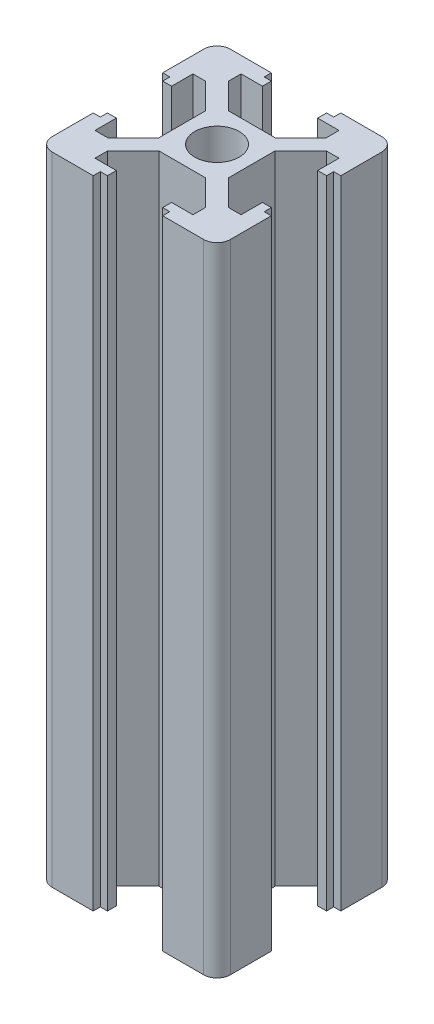
SolidWorks part; units mm, degrees
material "6063-O"
ref_plane "Front Plane" through (0, 0, 0) normal (0, 0, 1) x (1, 0, 0)
ref_plane "Top Plane" through (0, 0, 0) normal (0, 1, 0) x (1, 0, 0)
ref_plane "Right Plane" through (0, 0, 0) normal (1, 0, 0) x (0, 0, -1)
sketch "Sketch1" plane through (0, 0, 0) normal (0, 1, 0) x (1, 0, 0)
  line L0 (0, 14.5399) -> (0, 10) construction
  line L1 (-16.8658, 0) -> (2.5, 0) construction
  line L2 (13.2784, 3.9) -> (3.9, 3.9) construction
  line L3 (0, 0) -> (2.5, 0)
  line L4 (0, 0) -> (0, 2.5)
  line L5 (3.9, 10) -> (8.5, 10)
  line L6 (9.2, 0) -> (16.4291, 0) construction
  line L7 (-2.63, 3.9) -> (2.63, 3.9)
  line L9 (2.5491, 3.9) -> (2.63, 3.9)
  line L10 (3.9, 0) -> (3.9, 2.63)
  line L11 (13.2784, 3.1) -> (2.5491, 3.1) construction
  line L12 (8.2, 7.5573) -> (8.2, -3.0868) construction
  line L13 (9.2, 7.2593) -> (9.2, -8.1534) construction
  line L14 (10, 3.9) -> (9.2, 3.9)
  line L15 (9.2, 3.9) -> (9.2, 3.1)
  line L16 (9.2, 3.1) -> (8.2, 3.1)
  line L17 (8.2, 3.1) -> (8.2, 5.5)
  line L18 (8.2, 5.5) -> (6.77, 5.5)
  line L19 (6.77, 5.5) -> (3.9, 2.63)
  line L20 (5.0973, 5.5) -> (13.0082, 5.5) construction
  line L21 (3.1, 11.2046) -> (3.1, 2.6994) construction
  line L22 (3.9, 10.7498) -> (3.9, 3.9) construction
  line L23 (5.5, 11.523) -> (5.5, 1.4941) construction
  line L24 (-2.2597, 8.2) -> (6.1545, 8.2) construction
  line L25 (-2.9419, 9.2) -> (5.7225, 9.2) construction
  line L26 (3.9, 10) -> (3.9, 9.2)
  line L27 (3.9, 9.2) -> (3.1, 9.2)
  line L28 (3.1, 9.2) -> (3.1, 8.2)
  line L29 (3.1, 8.2) -> (5.5, 8.2)
  line L30 (5.5, 8.2) -> (5.5, 6.77)
  line L31 (5.5, 6.77) -> (2.63, 3.9)
  line L32 (0, 2.5) -> (0, -14.4122) construction
  line L33 (10, 3.9) -> (10, 8.5)
  line L34 (9.2, 0) -> (10, 0)
  line L35 (2.63, 3.9) -> (2.5491, 3.9) construction
  line L36 (3.9, 2.63) -> (3.9, 2.0627) construction
  line L37 (10, -3.9) -> (10, -8.5)
  line L38 (3.9, -10) -> (8.5, -10)
  line L39 (3.9, -10) -> (3.9, -9.2)
  line L40 (3.9, -9.2) -> (3.1, -9.2)
  line L41 (3.1, -9.2) -> (3.1, -8.2)
  line L42 (3.1, -8.2) -> (5.5, -8.2)
  line L43 (5.5, -8.2) -> (5.5, -6.77)
  line L44 (5.5, -6.77) -> (2.63, -3.9)
  line L45 (0, -3.9) -> (2.63, -3.9)
  line L46 (3.9, 0) -> (3.9, -2.63)
  line L47 (6.77, -5.5) -> (3.9, -2.63)
  line L48 (8.2, -5.5) -> (6.77, -5.5)
  line L49 (8.2, -3.1) -> (8.2, -5.5)
  line L50 (9.2, -3.1) -> (8.2, -3.1)
  line L51 (9.2, -3.9) -> (9.2, -3.1)
  line L52 (10, -3.9) -> (9.2, -3.9)
  line L53 (-3.9, -10) -> (-8.5, -10)
  line L54 (-10, -3.9) -> (-10, -8.5)
  line L55 (-10, -3.9) -> (-9.2, -3.9)
  line L56 (-9.2, -3.9) -> (-9.2, -3.1)
  line L57 (-9.2, -3.1) -> (-8.2, -3.1)
  line L58 (-8.2, -3.1) -> (-8.2, -5.5)
  line L59 (-8.2, -5.5) -> (-6.77, -5.5)
  line L60 (-6.77, -5.5) -> (-3.9, -2.63)
  line L61 (-3.9, 0) -> (-3.9, -2.63)
  line L62 (0, -3.9) -> (-2.63, -3.9)
  line L63 (-5.5, -6.77) -> (-2.63, -3.9)
  line L64 (-5.5, -8.2) -> (-5.5, -6.77)
  line L65 (-3.1, -8.2) -> (-5.5, -8.2)
  line L66 (-3.1, -9.2) -> (-3.1, -8.2)
  line L67 (-3.9, -9.2) -> (-3.1, -9.2)
  line L68 (-3.9, -10) -> (-3.9, -9.2)
  line L69 (-10, 3.9) -> (-10, 8.5)
  line L70 (-3.9, 10) -> (-8.5, 10)
  line L71 (-3.9, 10) -> (-3.9, 9.2)
  line L72 (-3.9, 9.2) -> (-3.1, 9.2)
  line L73 (-3.1, 9.2) -> (-3.1, 8.2)
  line L74 (-3.1, 8.2) -> (-5.5, 8.2)
  line L75 (-5.5, 8.2) -> (-5.5, 6.77)
  line L76 (-5.5, 6.77) -> (-2.63, 3.9)
  line L78 (-3.9, 0) -> (-3.9, 2.63)
  line L79 (-6.77, 5.5) -> (-3.9, 2.63)
  line L80 (-8.2, 5.5) -> (-6.77, 5.5)
  line L81 (-8.2, 3.1) -> (-8.2, 5.5)
  line L82 (-9.2, 3.1) -> (-8.2, 3.1)
  line L83 (-9.2, 3.9) -> (-9.2, 3.1)
  line L84 (-10, 3.9) -> (-9.2, 3.9)
  line L85 (0, 3.9) -> (-2.63, 3.9) [skipped]
  circle A0 centre (0, 0) radius 2.5
  arc A1 (8.5, 10) -> (10, 8.5) centre (8.5, 8.5) cw
  arc A2 (10, -8.5) -> (8.5, -10) centre (8.5, -8.5) cw
  arc A4 (-8.5, -10) -> (-10, -8.5) centre (-8.5, -8.5) cw
  arc A6 (-10, 8.5) -> (-8.5, 10) centre (-8.5, 8.5) cw
  point P12 (10, 10)
  point P126 (0, 0)
  dimension "D3" = 5
  dimension "D4" = 1.5
  dimension "D1" = 10
  dimension "D2" = 10
  dimension "D6" = 3.9
  dimension "D7" = 3.9
  dimension "D8" = 3.1
  dimension "D9" = 4
  dimension "D11" = 5.5
  dimension "D12" = 1.8
  dimension "D13" = 0.8
  dimension "D14" = 3.9
  dimension "D15" = 3.1
  dimension "D16" = 5.5
  dimension "D17" = 1.27
  dimension "D18" = 1.27
  dimension "D19" = 1.27
  dimension "D20" = 1.27
extrude "Boss-Extrude1" add sketch "Sketch1" along normal blind 71.5 contours A6 L69 L84 L83 L82 L81 L80 L79 L78 L61 L60 L59 L58 L57 L56 L55 L54 A4 L53 L68 L67 L66 L65 L64 L63 L62 L45 L44 L43 L42 L41 L40 L39 L38 A2 L37 L52 L51 L50 L49 L48 L47 L46 L10 L19 L18 L17 L16 L15 L14 L33
